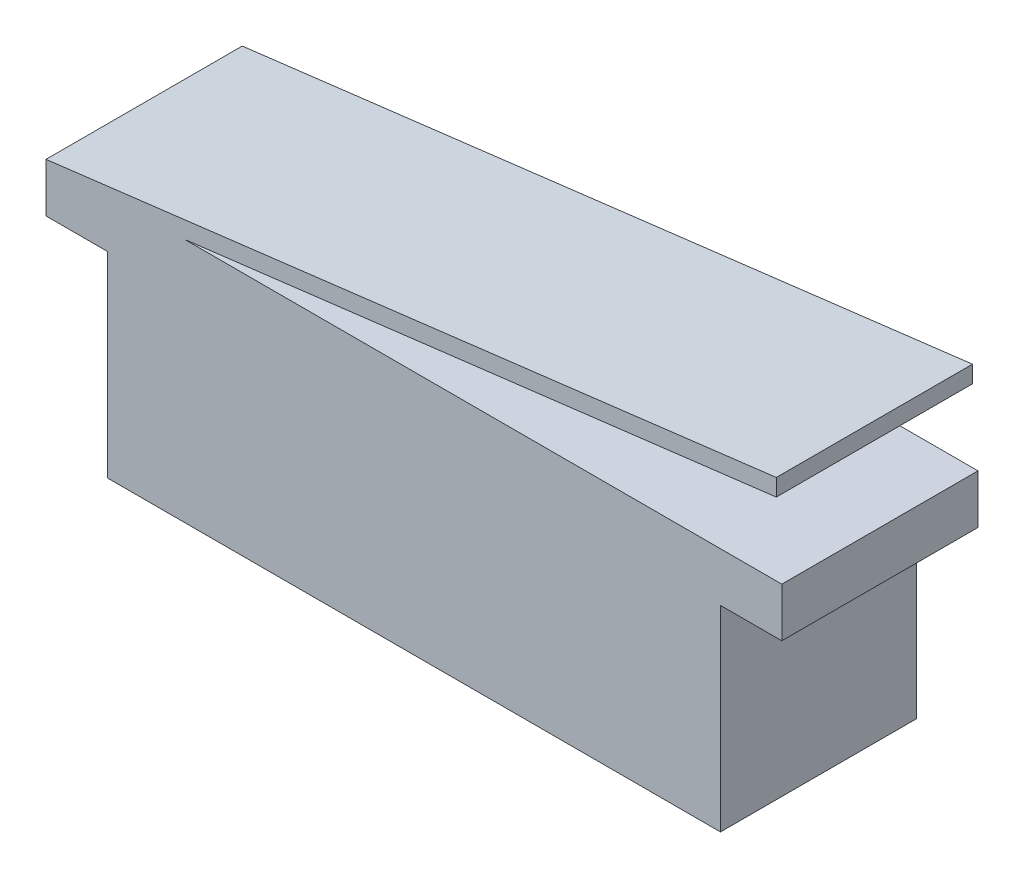
SolidWorks part; units mm, degrees
ref_plane "Front Plane" through (0, 0, 0) normal (0, 0, 1) x (1, 0, 0)
ref_plane "Top Plane" through (0, 0, 0) normal (0, 1, 0) x (1, 0, 0)
ref_plane "Right Plane" through (0, 0, 0) normal (1, 0, 0) x (0, 0, -1)
sketch "Sketch1" plane through (0, 0, 0) normal (0, 0, 1) x (1, 0, 0)
  line L0 (-15, 6) -> (14.7764, 9.6561)
  line L1 (-12.5, -4) -> (12.5, -4)
  line L2 (-12.5, -4) -> (-12.5, 4)
  line L3 (-12.5, 4) -> (12.5, 4)
  line L4 (12.5, -4) -> (12.5, 4)
  line L5 (-12.5, -4) -> (12.5, 4) construction
  line L6 (-12.5, 4) -> (12.5, -4) construction
  line L11 (-15, 4) -> (15, 4)
  line L12 (-15, 4) -> (-15, 6)
  line L13 (-15, 6) -> (15, 6)
  line L14 (15, 4) -> (15, 6)
  line L15 (-15, 4) -> (15, 6) construction
  line L16 (-15, 6) -> (15, 4) construction
  line L17 (-9.3462, 6) -> (14.7764, 8.9619)
  line L18 (14.7764, 9.6561) -> (14.7764, 8.9619)
  point P0 (0, 0)
  point P5 (0, 5)
  dimension "D1" = 25
  dimension "D2" = 8
  dimension "D3" = 30
  dimension "D4" = 12.5
  dimension "D5" = 1
  dimension "D6" = 2
  dimension "D7" = 7
  dimension "D8" = 30
  dimension "D9" = 24.3037
extrude "Boss-Extrude1" add sketch "Sketch1" along normal blind 8 contours L18 L0 L13 L17 | L11 L14 L13 L12 L3 | L1 L4 L3 L2
